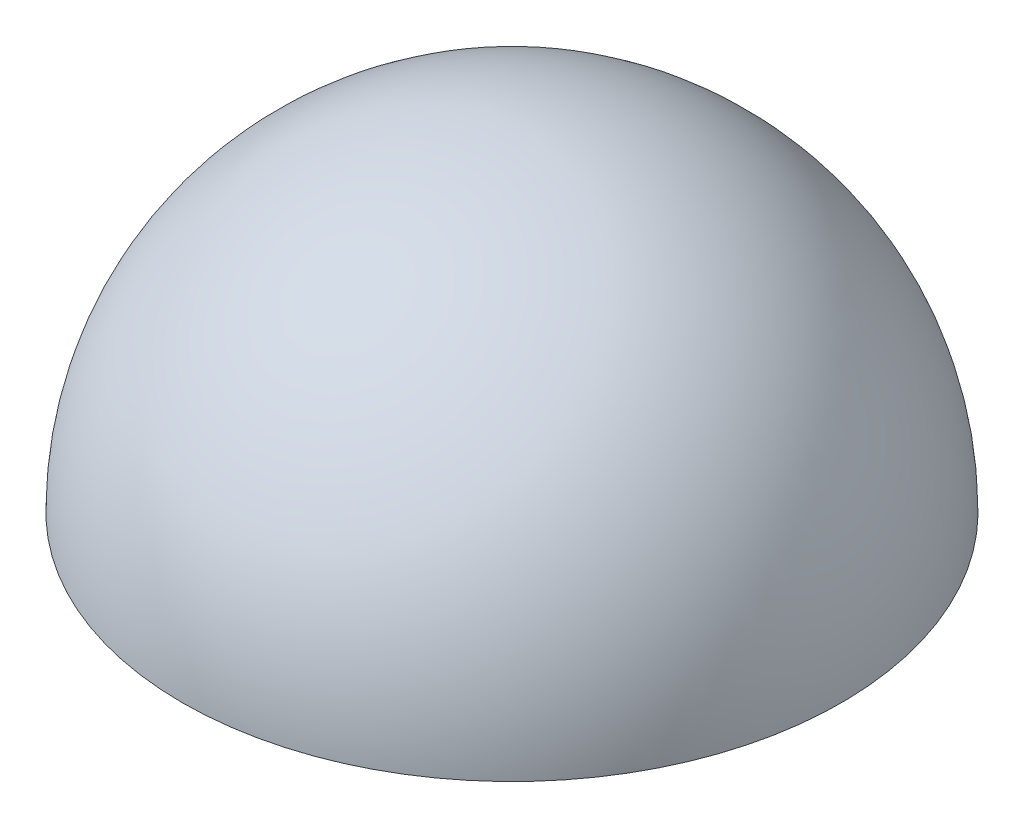
SolidWorks part; units mm, degrees
material "PVC Rigid"
ref_plane "Front Plane" through (0, 0, 0) normal (0, 0, 1) x (1, 0, 0)
ref_plane "Top Plane" through (0, 0, 0) normal (0, 1, 0) x (1, 0, 0)
ref_plane "Right Plane" through (0, 0, 0) normal (1, 0, 0) x (0, 0, -1)
sketch "Sketch2" plane through (0, 0, 0) normal (1, 0, 0) x (0, 0, -1)
  line L0 (0, 20) -> (0, 0)
  line L1 (0, 0) -> (-20, 0)
  arc A0 (0, 20) -> (-20, 0) centre (0, 0) ccw
  dimension "D1" = 20
ref_axis "Axis1" through (0, 1.617, 0) along (0, -1, 0)
revolve "Revolve2" add sketch "Sketch2" angle 360 about axis through (0, 1.617, 0) along (0, -1, 0)
sketch "Sketch3" plane through (0, 0, 0) normal (1, 0, 0) x (0, 0, -1)
  line L0 (0, 19.6) -> (0, 0)
  line L1 (0, 0) -> (-19.6, 0)
  line L2 (-20, 0) -> (20, 0) construction
  line L5 (-40, 0) -> (40, 0)
  arc A0 (-19.6, 0) -> (0, 19.6) centre (0, 0) cw
  arc A1 (20, 0) -> (-20, 0) centre (0, 0) ccw construction
  dimension "D2" = 0.4
revolve "Cut-Revolve1" cut sketch "Sketch3" angle 360 about L0
